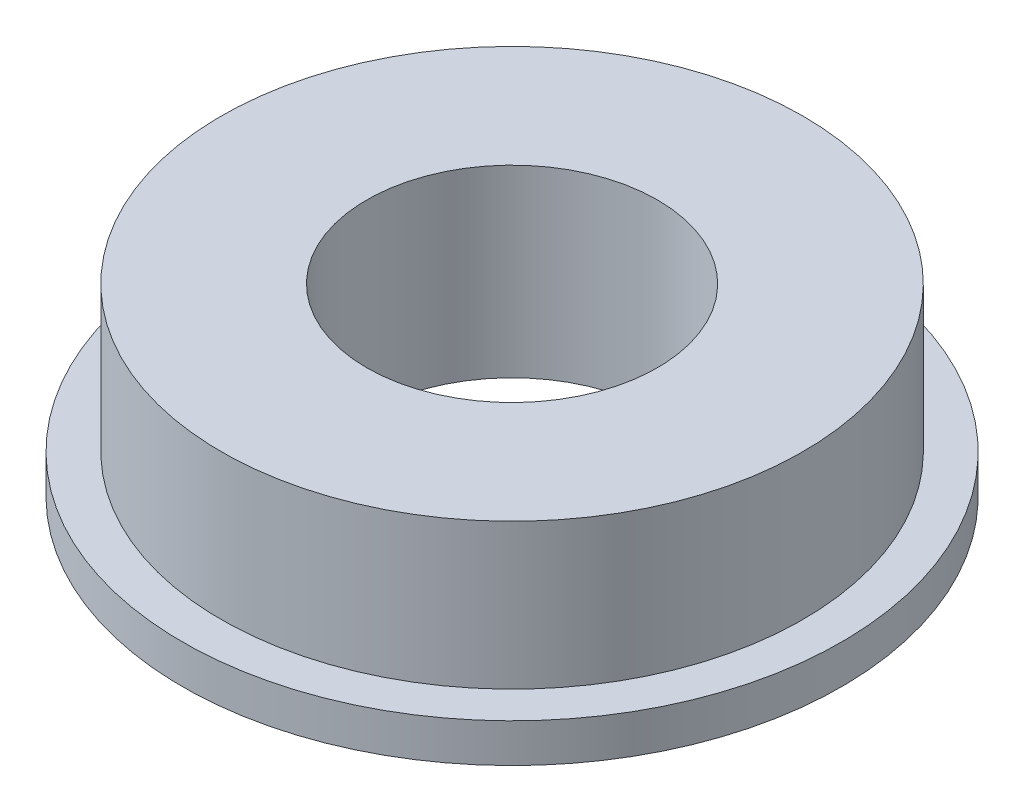
SolidWorks part; units mm, degrees
material "合金钢"
ref_plane "前视基准面" through (0, 0, 0) normal (0, 0, 1) x (1, 0, 0)
ref_plane "上视基准面" through (0, 0, 0) normal (0, 1, 0) x (1, 0, 0)
ref_plane "右视基准面" through (0, 0, 0) normal (1, 0, 0) x (0, 0, -1)
sketch "草图1" plane through (0, 0, 0) normal (0, 0, 1) x (1, 0, 0)
  line L0 (0, 0) -> (-3, 0)
  line L1 (-3, 0) -> (-6.8, 0)
  line L2 (-6.8, 0) -> (-6.8, 0.8)
  line L3 (-6.8, 0.8) -> (-6, 0.8)
  line L4 (-6, 0.8) -> (-6, 3.8)
  line L5 (-6, 3.8) -> (-3, 3.8)
  line L6 (-3, 3.8) -> (-3, 0)
  line L7 (0, 0) -> (0, 4.2316) construction
  dimension "D1" = 6
  dimension "D2" = 12
  dimension "D3" = 13.6
  dimension "D4" = 3
  dimension "D5" = 0.8
revolve "旋转1" add sketch "草图1" angle 360 about L7
